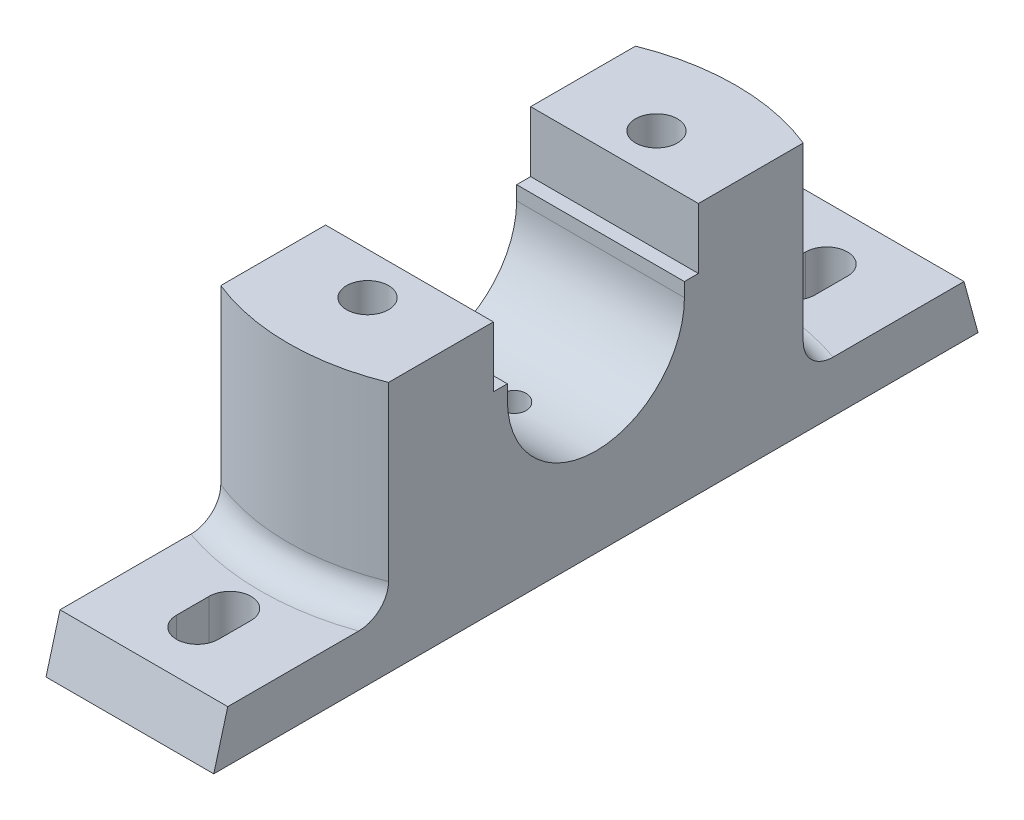
SolidWorks part; units mm, degrees
ref_plane "Front Plane" through (0, 0, 0) normal (0, 0, 1) x (1, 0, 0)
ref_plane "Top Plane" through (0, 0, 0) normal (0, 1, 0) x (1, 0, 0)
ref_plane "Right Plane" through (0, 0, 0) normal (1, 0, 0) x (0, 0, -1)
sketch "Sketch1" plane through (0, 0, 0) normal (1, 0, 0) x (0, 0, -1)
  line L0 (0, 53.7652) -> (0, -76.0501) construction
  line L1 (-82, 0) -> (82, 0)
  line L2 (82, 0) -> (79, 11)
  line L3 (79, 11) -> (50, 11)
  line L4 (50, 11) -> (50, 54)
  line L5 (50, 54) -> (22, 54)
  line L6 (22, 54) -> (22, 41)
  line L7 (22, 41) -> (19, 41)
  line L8 (-19, 38) -> (-19, 41)
  line L9 (-22, 54) -> (-22, 41)
  line L10 (-50, 54) -> (-22, 54)
  line L11 (-50, 11) -> (-50, 54)
  line L12 (-79, 11) -> (-50, 11)
  line L13 (-82, 0) -> (-79, 11)
  line L14 (19, 38) -> (19, 41)
  line L15 (-22, 41) -> (-19, 41)
  arc A0 (19, 38) -> (-19, 38) centre (0, 38) cw
  point P19 (0, 0)
  dimension "D6" = 16
  dimension "D8" = 50
  dimension "D9" = 19
  dimension "D1" = 164
  dimension "D2" = 3
  dimension "D3" = 11
  dimension "D4" = 44
  dimension "D5" = 54
  dimension "D7" = 13
extrude "Boss-Extrude1" add sketch "Sketch1" along normal mid plane 36 contours L1 L2 L3 L4 L5 L6 L7 L14 A0 L8 L15 L9 L10 L11 L12 L13
ref_plane "Plane1" through (0, 54, 0) normal (0, 1, 0) x (1, 0, 0)
sketch "Sketch2" plane through (0, 54, 0) normal (0, 1, 0) x (1, 0, 0)
  line L0 (-18, 50) -> (-18, 22) construction
  line L1 (18, 50) -> (-18, 50) construction
  line L2 (18, 50) -> (18, 22) construction
  line L3 (-18, 50) -> (-18, 44.4972)
  line L4 (18, 50) -> (-18, 50)
  line L5 (18, 50) -> (18, 44.4972)
  line L6 (-52.7929, 0) -> (62.4873, 0) construction
  line L7 (18, -50) -> (18, -44.4972)
  line L8 (-18, -50) -> (-18, -44.4972)
  line L9 (18, -50) -> (-18, -50)
  arc A0 (18, 44.4972) -> (-18, 44.4972) centre (0, 0) ccw
  arc A1 (18, -44.4972) -> (-18, -44.4972) centre (0, 0) cw
  dimension "D1" = 96
extrude "Cut-Extrude1" cut sketch "Sketch2" against normal up to surface (43 mm away) up to face at (0, 11, -64.5)
sketch "Sketch3" plane through (0, 0, 0) normal (0, -1, 0) x (-1, 0, 0)
  line L0 (-66.9675, 0) -> (65.3385, 0) construction
  line L1 (-10, 21) -> (10, 21)
  line L2 (-10, 21) -> (-10, 41)
  line L3 (-10, 41) -> (10, 41)
  line L4 (10, 21) -> (10, 41)
  line L5 (-18, -82) -> (-18, 82) construction
  line L6 (10, -21) -> (10, -41)
  line L7 (-10, -41) -> (10, -41)
  line L8 (-10, -21) -> (-10, -41)
  line L9 (-10, -21) -> (10, -21)
  dimension "D1" = 20
  dimension "D2" = 20
  dimension "D3" = 41
  dimension "D4" = 8
extrude "Cut-Extrude4" cut sketch "Sketch3" against normal blind 8
sketch "Sketch5" plane through (0, 8, 0) normal (0, -1, 0) x (-1, 0, 0)
  line L0 (-30.5059, 0) -> (46.1598, 0) construction
  line L1 (10, 21) -> (10, 41) construction
  circle A0 centre (0, 31) radius 4.5
  circle A1 centre (0, -31) radius 4.5
  dimension "D1" = 9
  dimension "D2" = 31
  dimension "D3" = 10
extrude "Cut-Extrude5" cut sketch "Sketch5" against normal through all
sketch "Sketch6" plane through (0, 0, 0) normal (0, -1, 0) x (-1, 0, 0)
  line L0 (-27.1422, 0) -> (38.2077, 0) construction
  line L1 (0, 60.5) -> (0, 67.5) construction
  line L2 (-4.5, 60.5) -> (-4.5, 67.5)
  line L3 (4.5, 60.5) -> (4.5, 67.5)
  line L4 (0, -60.5) -> (0, -67.5) construction
  line L5 (-4.5, -60.5) -> (-4.5, -67.5)
  line L6 (4.5, -60.5) -> (4.5, -67.5)
  arc A0 (-4.5, 60.5) -> (4.5, 60.5) centre (0, 60.5) ccw
  arc A1 (4.5, 67.5) -> (-4.5, 67.5) centre (0, 67.5) ccw
  arc A2 (-4.5, -60.5) -> (4.5, -60.5) centre (0, -60.5) cw
  arc A3 (4.5, -67.5) -> (-4.5, -67.5) centre (0, -67.5) cw
  point P5 (0, 64)
  point P12 (0, -64)
  dimension "D1" = 16
  dimension "D2" = 9
  dimension "D3" = 64
extrude "Cut-Extrude6" cut sketch "Sketch6" against normal through all
hole_wizard "Ø6.0mm Dowel Hole1" positions "3DSketch2" profile "Sketch8" hole size "Ø6.0" standard "ANSI Metric"
sketch3d "3DSketch2"
  point P0 (0, 19, 0)
  point P2 (0, 19, 0)
  dimension "D1" = 0
  dimension "D2" = 0
sketch "Sketch8" plane through (0, 19, 0) normal (1, 0, 0) x (0, 0, 1)
  line L0 (0, 0) -> (0, 7.8026)
  line L1 (0, 7.8026) -> (3, 6)
  line L2 (3, 6) -> (3, 0)
  line L5 (3, 0) -> (0, 0)
  line L10 (0, 7.8026) -> (-3, 6) construction
  line L11 (0, -6.35) -> (0, 107.95) construction
  dimension "Hole Dia." = 6
  dimension "Hole Depth" = 6
  dimension "Drill Angle" = 118
fillet "Fillet1" radius 6 1 edges at (0, 11, 48)
fillet "Fillet2" radius 6 1 edges at (0, 11, -48)
